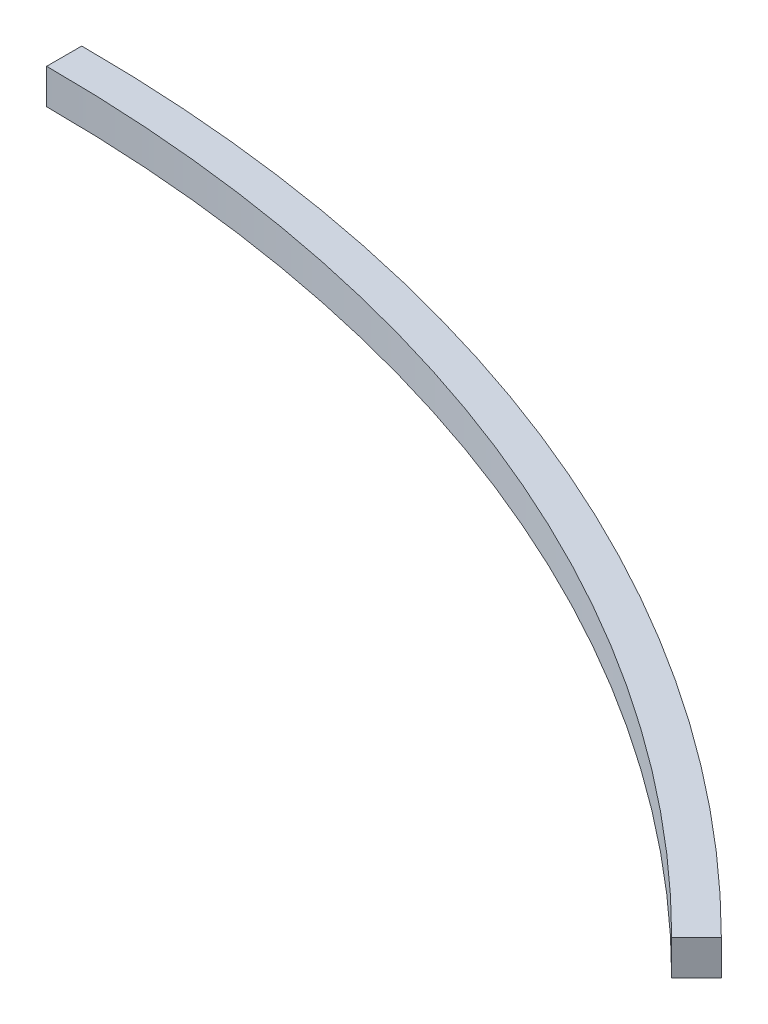
SolidWorks part; units mm, degrees
ref_plane "Front Plane" through (0, 0, 0) normal (0, 0, 1) x (1, 0, 0)
ref_plane "Top Plane" through (0, 0, 0) normal (0, 1, 0) x (1, 0, 0)
ref_plane "Right Plane" through (0, 0, 0) normal (1, 0, 0) x (0, 0, -1)
sketch "Sketch1" plane through (0, 0, 0) normal (0, 1, 0) x (1, 0, 0)
  line L0 (0, 0) -> (0, 430) construction
  line L1 (0, 430) -> (0, 440)
  line L2 (0, 0) -> (311.127, 311.127) construction
  line L3 (304.0559, 304.0559) -> (311.127, 311.127)
  arc A0 (0, 430) -> (304.0559, 304.0559) centre (0, 0) cw
  arc A1 (0, 440) -> (311.127, 311.127) centre (0, 0) cw
  dimension "D1" = 430
  dimension "D2" = 10
  dimension "D3" = 45
  dimension "D4" = 440
extrude "Boss-Extrude1" add sketch "Sketch1" along normal blind 10 contours A1 L1 A0 L3
